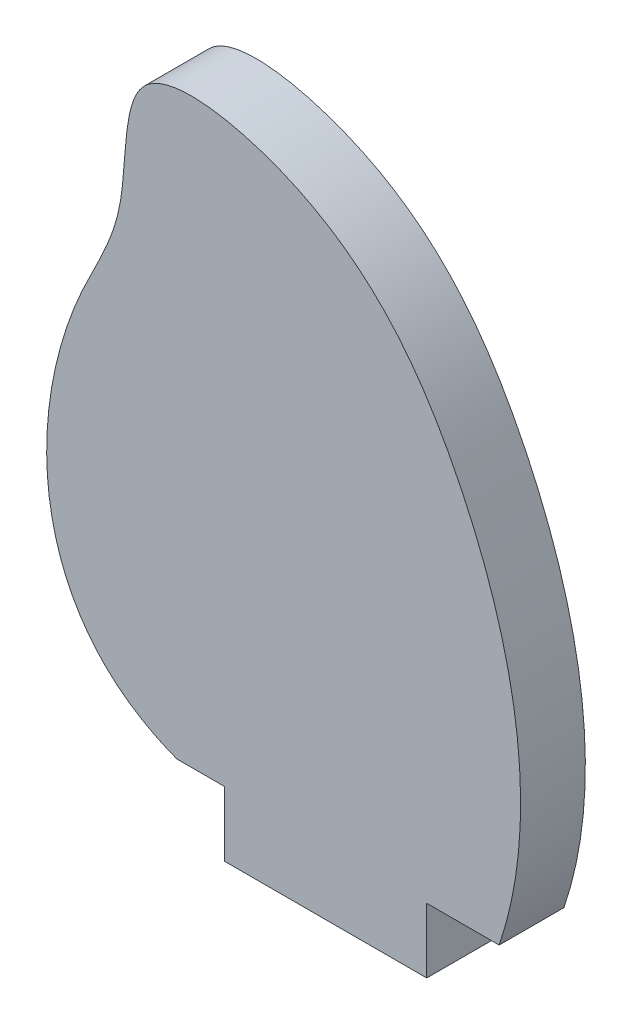
SolidWorks part; units mm, degrees
ref_plane "Front Plane" through (0, 0, 0) normal (0, 0, 1) x (1, 0, 0)
ref_plane "Top Plane" through (0, 0, 0) normal (0, 1, 0) x (1, 0, 0)
ref_plane "Right Plane" through (0, 0, 0) normal (1, 0, 0) x (0, 0, -1)
sketch "Sketch1" plane through (0, 0, 0) normal (0, 0, 1) x (1, 0, 0)
  line L0 (0, 0) -> (-2.3482, 0)
  line L1 (55, 0) -> (-55, 0) construction
  line L2 (13.5809, 0) -> (10, 0)
  line L3 (10, 0) -> (10, -3.2)
  line L4 (10, -3.2) -> (0, -3.2)
  line L5 (0, -55) -> (0, 55) construction
  line L6 (0, -3.2) -> (0, 0)
  spline S0 degree 3 poles (-2.3482, 0) (-9.9649, 2.8672) (-9.7931, 13.6701) (-4.5265, 22.1225) (-5.4338, 29.717) (5.695, 27.8153) (13.4855, 17.7672) (15.7685, 6.4603) (13.5809, 0) knots 0 0 0 0 0.289811 0.359115 0.444366 0.539446 0.71405 1 1 1 1
  dimension "D1" = 10
  dimension "D2" = 3.2
extrude "Boss-Extrude1" add sketch "Sketch1" along normal blind 3.2
